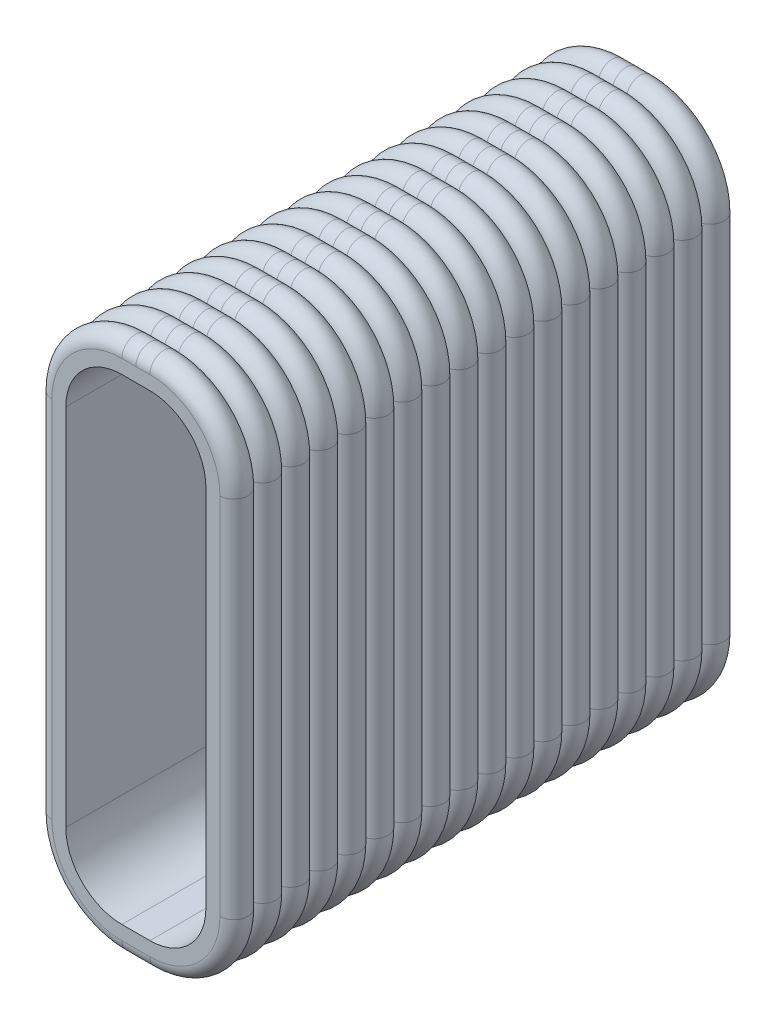
SolidWorks part; units mm, degrees
material "Copper-Cobalt-Beryllium alloy, UNS C17500"
ref_plane "Front Plane" through (0, 0, 0) normal (0, 0, 1) x (1, 0, 0)
ref_plane "Top Plane" through (0, 0, 0) normal (0, 1, 0) x (1, 0, 0)
ref_plane "Right Plane" through (0, 0, 0) normal (1, 0, 0) x (0, 0, -1)
sketch "Sketch1" plane through (0, 0, 0) normal (0, 0, 1) x (1, 0, 0)
  line L0 (-1.75, 3.25) -> (-1.75, -3.25)
  line L1 (-0.25, 4.25) -> (0.25, 4.25)
  line L2 (-1.25, 3.25) -> (-1.25, -3.25)
  line L3 (-0.25, -4.25) -> (0.25, -4.25)
  line L4 (1.25, 3.25) -> (1.25, -3.25)
  line L5 (-1.25, 4.25) -> (1.25, -4.25) construction
  line L6 (-1.25, -4.25) -> (1.25, 4.25) construction
  line L7 (-0.25, -4.75) -> (0.25, -4.75)
  line L8 (1.75, 3.25) -> (1.75, -3.25)
  line L9 (-0.25, 4.75) -> (0.25, 4.75)
  arc A2 (0.25, -4.25) -> (1.25, -3.25) centre (0.25, -3.25) ccw
  arc A3 (-1.25, -3.25) -> (-0.25, -4.25) centre (-0.25, -3.25) ccw
  arc A4 (0.25, 4.25) -> (1.25, 3.25) centre (0.25, 3.25) cw
  arc A5 (-0.25, 4.25) -> (-1.25, 3.25) centre (-0.25, 3.25) ccw
  arc A6 (-1.75, -3.25) -> (-0.25, -4.75) centre (-0.25, -3.25) ccw
  arc A7 (0.25, -4.75) -> (1.75, -3.25) centre (0.25, -3.25) ccw
  arc A8 (0.25, 4.75) -> (1.75, 3.25) centre (0.25, 3.25) cw
  arc A9 (-0.25, 4.75) -> (-1.75, 3.25) centre (-0.25, 3.25) ccw
  point P0 (0, 0)
  point P5 (-1.9876, 4.2218)
  point P9 (-1.4886, 3.92)
  point P10 (-1.4589, 3.9665)
  point P11 (0, 0)
  point P13 (0, 0)
  dimension "D2" = 1
  dimension "D1" = 2.5
  dimension "D3" = 6.5
  dimension "D4" = 0.5
extrude "Boss-Extrude1" add sketch "Sketch1" against normal blind 9
sketch "Sketch2" plane through (0, 0, 0) normal (1, 0, 0) x (0, 0, -1)
  line L0 (9, 4.75) -> (0, 4.75) construction
  line L1 (0, 4.75) -> (0.5, 4.75) construction
  line L3 (0.5, 4.75) -> (0.5, 4.5)
  line L4 (0, 4.75) -> (0, 4.5)
  line L6 (0, 4.75) -> (0, 5.25)
  line L7 (0, 5.25) -> (0.5, 5.25)
  line L8 (0.5, 5.25) -> (0.5, 4.75)
  arc A0 (0.5, 4.5) -> (0, 4.5) centre (0.25, 4.5) ccw
  point P1 (0, 0)
  point P6 (0, 0)
  point P7 (0, 0)
  point P10 (0, 0)
  point P13 (-4.25, 4.5)
  point P14 (0, 0)
  point P15 (0, 0)
  point P17 (0, 0)
  dimension "D1" = 0.5
  dimension "D2" = 0.5
sketch "Sketch3" plane through (0, 0, 0) normal (0, 0, 1) x (1, 0, 0)
  line L4 (0.25, 4.75) -> (-0.25, 4.75) construction
  line L5 (-1.75, 3.25) -> (-1.75, -3.25) construction
  line L6 (-0.25, -4.75) -> (0.25, -4.75) construction
  line L7 (1.75, -3.25) -> (1.75, 3.25) construction
  line L8 (0.25, 4.75) -> (-0.25, 4.75)
  line L9 (-1.75, 3.25) -> (-1.75, -3.25)
  line L10 (-0.25, -4.75) -> (0.25, -4.75)
  line L11 (1.75, -3.25) -> (1.75, 3.25)
  arc A4 (-0.25, 4.75) -> (-1.75, 3.25) centre (-0.25, 3.25) ccw construction
  arc A5 (-1.75, -3.25) -> (-0.25, -4.75) centre (-0.25, -3.25) ccw construction
  arc A6 (0.25, -4.75) -> (1.75, -3.25) centre (0.25, -3.25) ccw construction
  arc A7 (1.75, 3.25) -> (0.25, 4.75) centre (0.25, 3.25) ccw construction
  arc A8 (-0.25, 4.75) -> (-1.75, 3.25) centre (-0.25, 3.25) ccw
  arc A9 (-1.75, -3.25) -> (-0.25, -4.75) centre (-0.25, -3.25) ccw
  arc A10 (0.25, -4.75) -> (1.75, -3.25) centre (0.25, -3.25) ccw
  arc A11 (1.75, 3.25) -> (0.25, 4.75) centre (0.25, 3.25) ccw
sweep "Cut-Sweep3" cut profiles "Sketch2" path "Sketch3"
pattern_linear "LPattern1" count 18 spacing 0.5 along (0, 0, -1) of "Cut-Sweep3"
